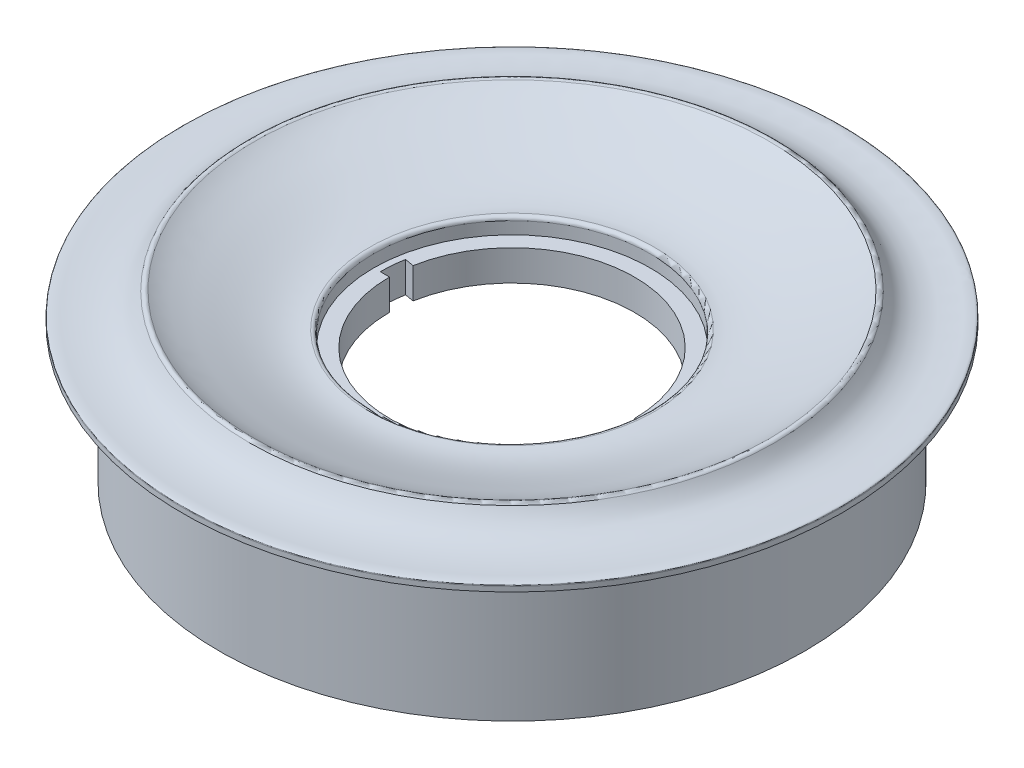
SolidWorks part; units mm, degrees
ref_plane "Front Plane" through (0, 0, 0) normal (0, 0, 1) x (1, 0, 0)
ref_plane "Top Plane" through (0, 0, 0) normal (0, 1, 0) x (1, 0, 0)
ref_plane "Right Plane" through (0, 0, 0) normal (1, 0, 0) x (0, 0, -1)
sketch "Sketch1" plane through (0, 0, 0) normal (0, 0, 1) x (1, 0, 0)
  line L0 (0, -26.8588) -> (0, 26.8588) construction
  line L1 (0, 0) -> (25.4, 0) construction
  line L2 (25.4, 0) -> (27.94, 0)
  line L3 (27.94, 0) -> (27.94, 3.81)
  line L4 (27.94, 3.81) -> (31.75, 3.81)
  line L5 (31.75, 3.81) -> (31.75, 7.62)
  line L6 (31.75, 7.62) -> (52.9506, 15.0818)
  line L7 (52.9506, 15.0818) -> (59.1779, 10.16)
  line L8 (59.1779, 10.16) -> (59.1779, -17.78)
  line L9 (59.1779, -17.78) -> (60.7019, -17.78)
  line L10 (60.7019, -17.78) -> (60.7019, 10.795)
  line L11 (60.7019, 10.795) -> (68.3219, 10.795)
  line L12 (68.3219, 11.811) -> (68.3219, 10.795)
  line L13 (68.3219, 10.795) -> (70.6387, 10.8021)
  line L14 (28.6702, 8.89) -> (28.6702, 6.35)
  line L15 (28.6702, 6.35) -> (25.4, 6.35)
  line L16 (25.4, 6.35) -> (25.4, 0)
  arc A0 (68.3017, 11.9856) -> (68.3219, 11.811) centre (67.5599, 11.811) cw
  arc A1 (54.4334, 16.4924) -> (53.3725, 16.7132) centre (53.7938, 16.0782) ccw
  arc A2 (28.6702, 8.89) -> (29.5282, 9.6459) centre (29.4322, 8.89) cw
  spline S0 degree 3 poles (29.5282, 9.6459) (32.3548, 9.287) (37.8008, 10.3) (43.8116, 12.5138) (48.9715, 14.4254) (51.772, 15.6512) (53.3725, 16.7132) knots 0.030766 0.030766 0.030766 0.030766 0.353803 0.633804 0.758493 0.97553 0.97553 0.97553 0.97553
  spline S1 degree 3 poles (54.4334, 16.4924) (55.1403, 15.4008) (56.6341, 13.4534) (61.085, 11.9245) (65.0465, 12.154) (67.3587, 12.3329) (68.2556, 12.1814) (68.3017, 11.9856) knots 0.032484 0.032484 0.032484 0.032484 0.240161 0.498483 0.829405 0.925193 0.958837 0.958837 0.958837 0.958837
  point P2 (0, 0)
  point P54 (56.0643, 12.6209)
  dimension "D18" = 0.762
  dimension "D2" = 0.762
  dimension "D3" = 0.762
  dimension "D6" = 33.8582
  dimension "D21" = 2.6427
  dimension "D25" = 25.1698
  dimension "D28" = 15.537
  dimension "D1" = 25.4
  dimension "D4" = 28.575
  dimension "D5" = 22.4754
  dimension "D7" = 6.35
  dimension "D8" = 7.9375
  dimension "D9" = 1.524
  dimension "D10" = 2.54
  dimension "D11" = 3.81
  dimension "D12" = 7.62
  dimension "D13" = 27.94
  dimension "D14" = 1.016
  dimension "D15" = 3.81
  dimension "D16" = 3.81
  dimension "D17" = 17.78
  dimension "D19" = 25.4
  dimension "D20" = 1.3053
  dimension "D22" = 1.4018
  dimension "D23" = 0.635
  dimension "D24" = 0.725
  dimension "D26" = 0.7121
  dimension "D27" = 2.54
revolve "Revolve1" add sketch "Sketch1" angle 360 about L0
sketch "Sketch2" plane through (0, 6.35, 0) normal (0, 1, 0) x (1, 0, 0)
  line L0 (28.6702, 0) -> (-28.6702, 0)
  line L1 (28.2201, -5.06) -> (-28.2201, 5.06)
  circle A0 centre (0, 0) radius 25.4
  circle A1 centre (0, 0) radius 28.6702
  circle A2 centre (0, 0) radius 28.6702 construction
  circle A3 centre (0, 0) radius 25.4 construction
  circle A4 centre (0, 0) radius 27.305
  circle M2 centre (0, 0) radius 25.4
  dimension "D2" = 54.61
  dimension "D1" = 5.08
extrude "Cut-Extrude2" cut sketch "Sketch2" against normal blind 25.4 contours L1 A4 L0 M2 | L1 A4 L0 M2 | A0
